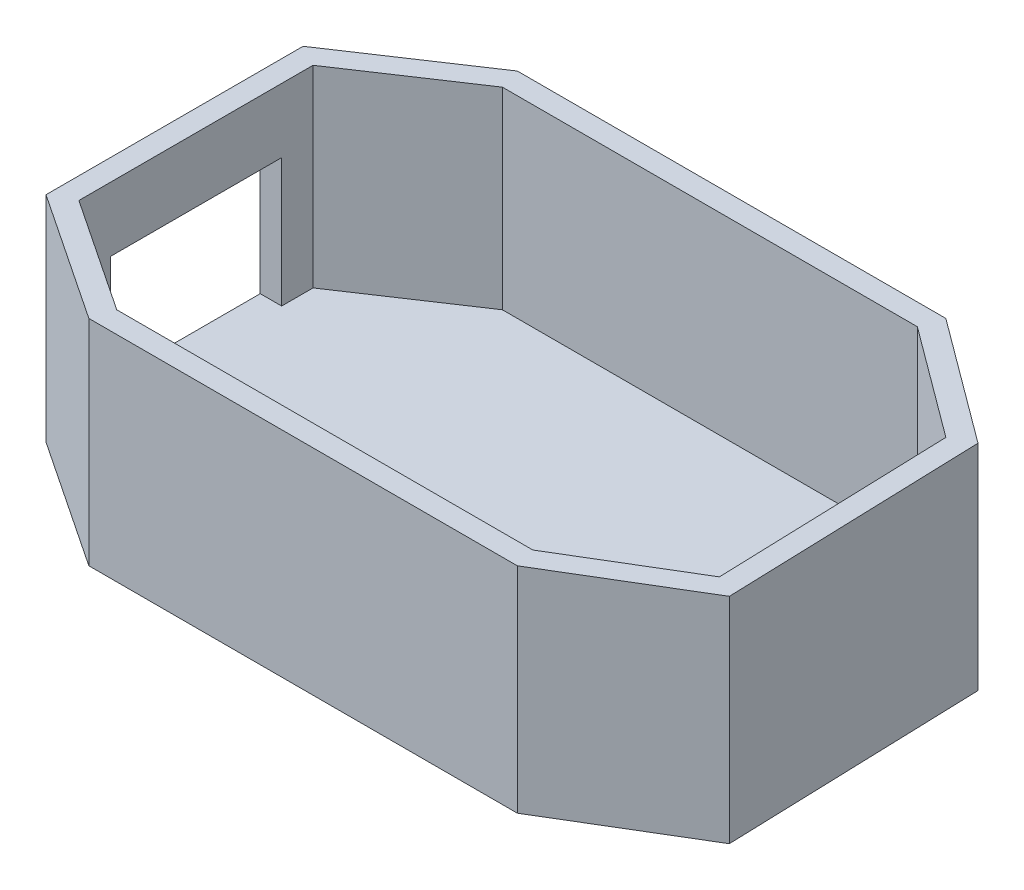
SolidWorks part; units mm, degrees
ref_plane "Płaszczyzna przednia" through (0, 0, 0) normal (0, 0, 1) x (1, 0, 0)
ref_plane "Płaszczyzna górna" through (0, 0, 0) normal (0, 1, 0) x (1, 0, 0)
ref_plane "Płaszczyzna prawa" through (0, 0, 0) normal (1, 0, 0) x (0, 0, -1)
sketch "Szkic1" plane through (0, 0, 0) normal (0, 1, 0) x (1, 0, 0)
  line L5 (-60, 40) -> (40, 40)
  line L6 (-90, 20) -> (-90, -40)
  line L8 (-60, 40) -> (-90, 20)
  line L10 (-90, -40) -> (-60, -60)
  line L13 (40, -60) -> (70.907, -41.4323)
  line L14 (70.907, -41.4323) -> (68.971, 18.5365)
  line L15 (68.971, 18.5365) -> (40, 40)
  line L17 (-60, -60) -> (40, -60)
  point P0 (0, 0)
  dimension "D4" = 60
  dimension "D1" = 100
  dimension "D2" = 100
  dimension "D3" = 60
  dimension "D5" = 36.0555
  dimension "D6" = 36.0555
  dimension "D7" = 36.0555
  dimension "D8" = 36.0555
extrude "Dodanie-wyciągnięcie2" add sketch "Szkic1" along normal blind 50 contours L5 L15 L14 L13 L17 L10 L6 L8
shell "Skorupa2" thickness 5
sketch "Szkic2" plane through (-90, 0, 0) normal (-1, 0, 0) x (0, 0, 1)
  line L0 (-20, 50) -> (40, 50) construction
  line L1 (-10, 35) -> (30, 35)
  line L2 (-10, 35) -> (-10, 5)
  line L3 (-10, 5) -> (30, 5)
  line L4 (30, 35) -> (30, 5)
  line L5 (-10, 35) -> (30, 5) construction
  line L6 (-10, 5) -> (30, 35) construction
  line L7 (-20, 0) -> (40, 0) construction
  line L8 (40, 50) -> (40, 0) construction
  line L9 (-20, 50) -> (-20, 0) construction
  point P0 (10, 20)
  dimension "D1" = 40
  dimension "D2" = 30
  dimension "D3" = 15
  dimension "D4" = 5
  dimension "D5" = 10
  dimension "D6" = 10
extrude "Wytnij-wyciągnięcie1" cut sketch "Szkic2" against normal up to next
